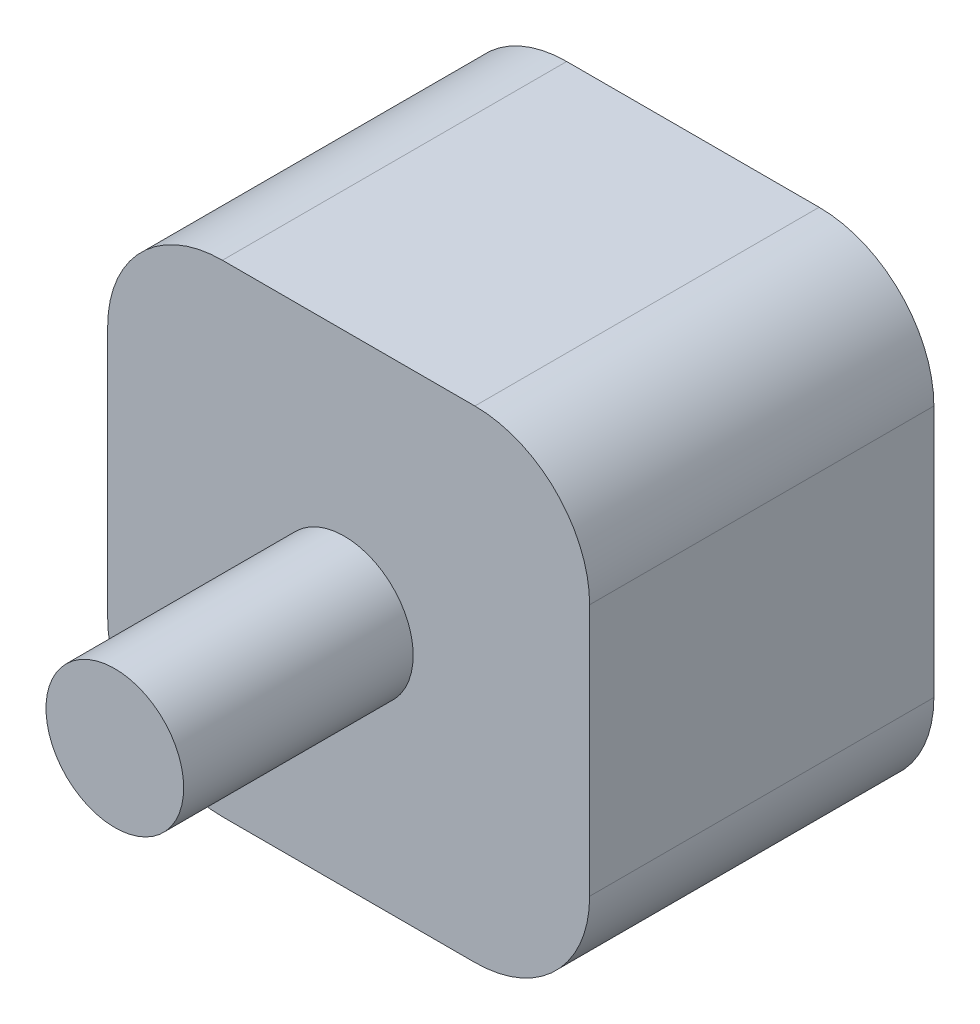
SolidWorks part; units mm, degrees
material "铸造合金钢"
ref_plane "前视基准面" through (0, 0, 0) normal (0, 0, 1) x (1, 0, 0)
ref_plane "上视基准面" through (0, 0, 0) normal (0, 1, 0) x (1, 0, 0)
ref_plane "右视基准面" through (0, 0, 0) normal (1, 0, 0) x (0, 0, -1)
sketch "草图1" plane through (0, 0, 0) normal (0, 0, 1) x (1, 0, 0)
  line L1 (-20.6234, 21.5105) -> (21.3766, 21.5105)
  line L2 (-20.6234, 21.5105) -> (-20.6234, -20.4895)
  line L3 (-20.6234, -20.4895) -> (21.3766, -20.4895)
  line L4 (21.3766, 21.5105) -> (21.3766, -20.4895)
extrude "凸台-拉伸1" add sketch "草图1" along normal blind 30 contours L2 L3 L4 L1
sketch "草图2" plane through (0, 0, 30) normal (0, 0, 1) x (1, 0, 0)
  circle A0 centre (0, 0) radius 6
extrude "凸台-拉伸2" add sketch "草图2" along normal blind 20 separate body contours A0
fillet "圆角2" radius 10 1 edges at (21.3766, 21.5105, 15)
fillet "圆角3" radius 10 1 edges at (-20.6234, 21.5105, 15)
fillet "圆角4" radius 10 1 edges at (-20.6234, -20.4895, 15)
fillet "圆角5" radius 10 1 edges at (21.3766, -20.4895, 15)
